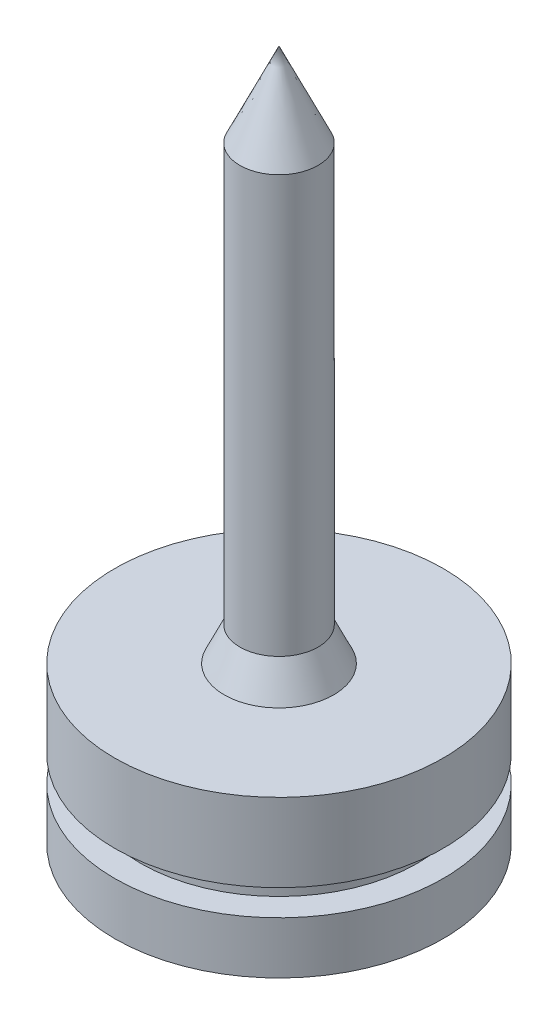
SolidWorks part; units mm, degrees
ref_plane "前视基准面" through (0, 0, 0) normal (0, 0, 1) x (1, 0, 0)
ref_plane "上视基准面" through (0, 0, 0) normal (0, 1, 0) x (1, 0, 0)
ref_plane "右视基准面" through (0, 0, 0) normal (1, 0, 0) x (0, 0, -1)
sketch "草图3" plane through (0, 0, 0) normal (1, 0, 0) x (0, 0, -1)
  line L0 (0, 0) -> (-31.5, 0)
  line L1 (-31.5, 0) -> (-31.5, 10)
  line L2 (-31.5, 10) -> (-26.5, 10)
  line L3 (-26.5, 10) -> (-26.5, 15)
  line L4 (-26.5, 15) -> (-31.5, 15)
  line L5 (-31.5, 15) -> (-31.5, 30)
  line L6 (-31.5, 30) -> (-10.5, 30)
  line L7 (-10.5, 30) -> (-7.5, 36.4335)
  line L8 (-7.5, 36.4335) -> (-7.5, 116.4335)
  line L9 (-7.5, 116.4335) -> (0, 132.5173)
  line L10 (0, 132.5173) -> (0, 0)
  point P12 (-7.4576, 96.5245)
  dimension "D1" = 31.5
  dimension "D2" = 10
  dimension "D3" = 5
  dimension "D4" = 15
  dimension "D5" = 5
  dimension "D6" = 21
  dimension "D7" = 65
  dimension "D8" = 7.5
  dimension "D9" = 80
revolve "旋转1" add sketch "草图3" angle 360 about L10
